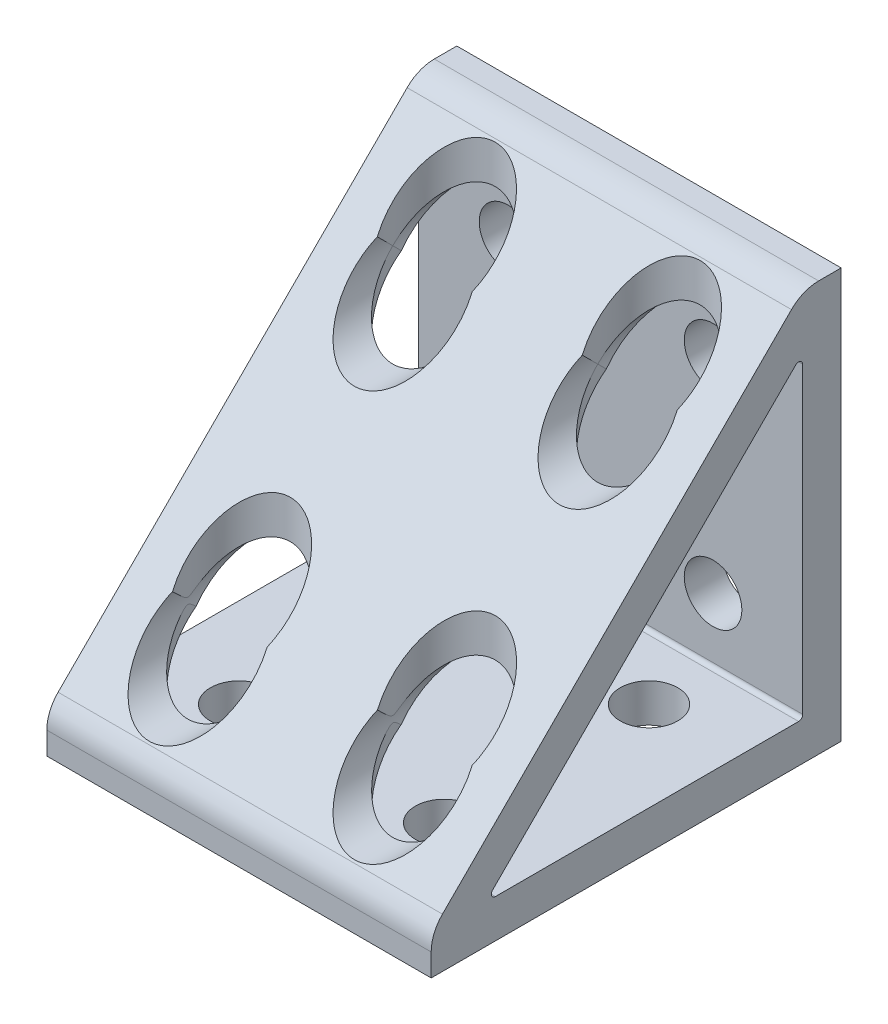
SolidWorks part; units mm, degrees
material "6105-T5 Aluminum"
ref_plane "Front Plane" through (0, 0, 0) normal (0, 0, 1) x (1, 0, 0)
ref_plane "Top Plane" through (0, 0, 0) normal (0, 1, 0) x (1, 0, 0)
ref_plane "Right Plane" through (0, 0, 0) normal (1, 0, 0) x (0, 0, -1)
sketch "Sketch1" plane through (0, 0, 0) normal (1, 0, 0) x (0, 0, -1)
  line L0 (-6.1574, 49.4051) -> (-49.4051, 6.1574)
  line L1 (-50.8, 0) -> (-50.8, 2.7898)
  line L2 (0, 0) -> (-50.8, 0)
  line L3 (0, 50.8) -> (0, 0)
  line L4 (0, 50.8) -> (-2.7898, 50.8)
  line L5 (-4.7625, 5.2705) -> (-4.7625, 42.8384)
  line L6 (-5.2705, 4.7625) -> (-42.8384, 4.7625)
  line L7 (-43.1976, 5.6297) -> (-5.6297, 43.1976)
  arc A0 (-49.4051, 6.1574) -> (-50.8, 2.7898) centre (-46.0375, 2.7898) ccw
  arc A1 (-2.7898, 50.8) -> (-6.1574, 49.4051) centre (-2.7898, 46.0375) ccw
  arc A2 (-4.7625, 42.8384) -> (-5.6297, 43.1976) centre (-5.2705, 42.8384) ccw
  arc A3 (-5.2705, 4.7625) -> (-4.7625, 5.2705) centre (-5.2705, 5.2705) ccw
  arc A4 (-43.1976, 5.6297) -> (-42.8384, 4.7625) centre (-42.8384, 5.2705) ccw
extrude "Boss-Extrude1" add sketch "Sketch1" along normal mid plane 47.625
hole_wizard "K (0.281) Diameter Hole3" positions "Sketch15" profile "Sketch14" hole size "K" standard "ANSI Inch"
sketch "Sketch15" plane through (0, 0, 0) normal (0, 0, -1) x (-1, 0, 0)
  line L0 (-23.8125, 0) -> (23.8125, 0) construction
  line L1 (-23.8125, 0) -> (-23.8125, 50.8) construction
  point P0 (-12.7, 12.7)
  point P2 (-12.7, 38.1)
  dimension "D1" = 12.7
  dimension "D2" = 25.4
  dimension "D3" = 11.1125
  dimension "D4" = 11.1125
sketch "Sketch14" plane through (12.7, 12.7, 0) normal (1, 0, 0) x (0, 1, 0)
  line L0 (0, 0) -> (0, 8.7483)
  line L1 (0, 8.7483) -> (3.5687, 6.604)
  line L2 (3.5687, 6.604) -> (3.5687, 0)
  line L5 (3.5687, 0) -> (0, 0)
  line L10 (0, 8.7483) -> (-3.5687, 6.604) construction
  line L11 (0, -6.35) -> (0, 107.95) construction
  dimension "Hole Dia." = 7.1374
  dimension "Hole Depth" = 6.604
  dimension "Drill Angle" = 118
sketch "Sketch18" plane through (0, 0, 4.7625) normal (0, 0, 1) x (1, 0, 0)
  circle A0 centre (12.7, 12.7) radius 6.35
  dimension "D1" = 12.7
extrude "Cut-Extrude15" cut sketch "Sketch18" along normal through all contours A0
sketch "Sketch19" plane through (0, 0, 4.7625) normal (0, 0, 1) x (1, 0, 0)
  circle A0 centre (12.7, 38.1) radius 6.35
  dimension "D1" = 12.7
extrude "Cut-Extrude16" cut sketch "Sketch19" along normal blind 27.94
hole_wizard "K (0.281) Diameter Hole4" positions "Sketch21" profile "Sketch20" hole size "K" standard "ANSI Inch"
sketch "Sketch21" plane through (0, 0, 0) normal (0, -1, 0) x (-1, 0, 0)
  line L0 (-23.8125, 0) -> (23.8125, 0) construction
  line L1 (-23.8125, -50.8) -> (-23.8125, 0) construction
  point P0 (-12.7, -12.7)
  point P2 (-12.7127, -38.1)
  dimension "D1" = 12.7
  dimension "D2" = 25.4
  dimension "D3" = 11.0998
  dimension "D4" = 11.1125
sketch "Sketch20" plane through (12.7, 0, 12.7) normal (1, 0, 0) x (0, 0, -1)
  line L0 (0, 0) -> (0, 8.7483)
  line L1 (0, 8.7483) -> (3.5687, 6.604)
  line L2 (3.5687, 6.604) -> (3.5687, 0)
  line L5 (3.5687, 0) -> (0, 0)
  line L10 (0, 8.7483) -> (-3.5687, 6.604) construction
  line L11 (0, -6.35) -> (0, 107.95) construction
  dimension "Hole Dia." = 7.1374
  dimension "Hole Depth" = 6.604
  dimension "Drill Angle" = 118
sketch "Sketch22" plane through (0, 4.7625, 0) normal (0, 1, 0) x (1, 0, 0)
  circle A0 centre (12.7, -12.7) radius 6.35
  dimension "D1" = 12.7
extrude "Cut-Extrude17" cut sketch "Sketch22" along normal blind 50.8
sketch "Sketch23" plane through (0, 4.7625, 0) normal (0, 1, 0) x (1, 0, 0)
  circle A0 centre (12.7127, -38.1) radius 6.35
  dimension "D1" = 12.7
extrude "Cut-Extrude18" cut sketch "Sketch23" along normal blind 50.8
pattern_linear "LPattern2" count 2 spacing 25.4 along (-1, 0, 0) of "Cut-Extrude15", "Cut-Extrude16", "K (0.281) Diameter Hole4", "Cut-Extrude17", "Cut-Extrude18", "K (0.281) Diameter Hole3"
